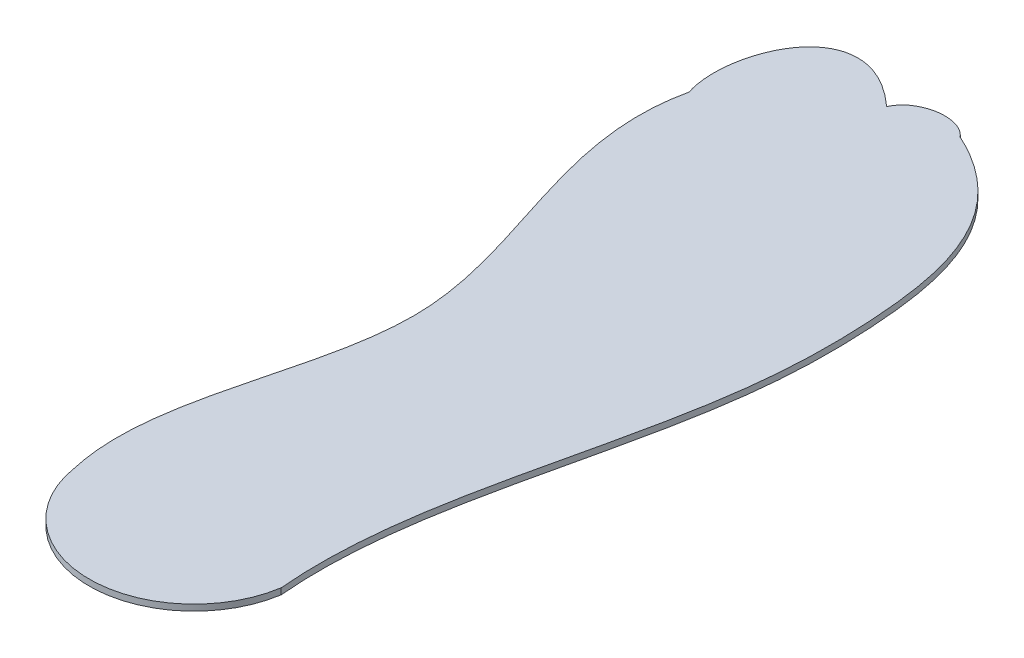
SolidWorks part; units mm, degrees
ref_plane "Front Plane" through (0, 0, 0) normal (0, 0, 1) x (1, 0, 0)
ref_plane "Top Plane" through (0, 0, 0) normal (0, 1, 0) x (1, 0, 0)
ref_plane "Right Plane" through (0, 0, 0) normal (1, 0, 0) x (0, 0, -1)
sketch "Sketch1" plane through (0, 0, 0) normal (0, 1, 0) x (1, 0, 0)
  arc A0 (-40.6792, -103.2215) -> (26.9101, -103.2215) centre (-6.8846, -97.9138) ccw
  spline S0 degree 3 poles (-46.6792, 103.5874) (-52.7858, 121.9074) (-38.637, 157.5744) (-10.2962, 131.7044) knots 0 0 0 0 1 1 1 1
  spline S1 degree 3 poles (-10.2962, 131.7044) (-7.2527, 138.9749) (5.2805, 141.1935) (10.3208, 135.0874) knots 0 0 0 0 1 1 1 1
  spline S2 degree 3 poles (10.3208, 135.0874) (39.4026, 121.7879) (48.0958, 85.9318) (48.3636, 1.7437) (22.5703, -55.2447) (26.9101, -103.2215) knots 0 0 0 0 0.296821 0.429544 1 1 1 1
  spline S3 degree 3 poles (-40.6792, -103.2215) (-48.4247, -69.4646) (-5.3125, -0.2759) (-54.797, 67.4699) (-46.6792, 103.5874) knots 0 0 0 0 0.483382 1 1 1 1
  point P0 (0, 0)
  dimension "D1" = 254.6502
  dimension "D2" = 68.013
  dimension "D3" = 24.253
  dimension "D4" = 210.9691
  dimension "D5" = 34.2089
  dimension "D9" = 8.8652
  dimension "D6" = 97.9138
  dimension "D7" = 103.2215
  dimension "D8" = 103.2215
  dimension "D10" = 10.3208
  dimension "D11" = 26.3208
  dimension "D12" = 26.9101
  dimension "D13" = 45.3208
  dimension "D14" = 47.3208
  dimension "D15" = 4.6784
  dimension "D16" = 10.2962
  dimension "D17" = 28.3814
  dimension "D18" = 35.7611
  dimension "D19" = 35.9858
  dimension "D20" = 46.6792
  dimension "D21" = 34.5874
  dimension "D22" = 38.6743
  dimension "D23" = 72.0874
  dimension "D24" = 88.0874
  dimension "D25" = 103.5874
  dimension "D26" = 123.3494
  dimension "D27" = 131.7044
  dimension "D28" = 136.4799
  dimension "D29" = 2.9126
extrude "Boss-Extrude1" add sketch "Sketch1" along normal blind 2
